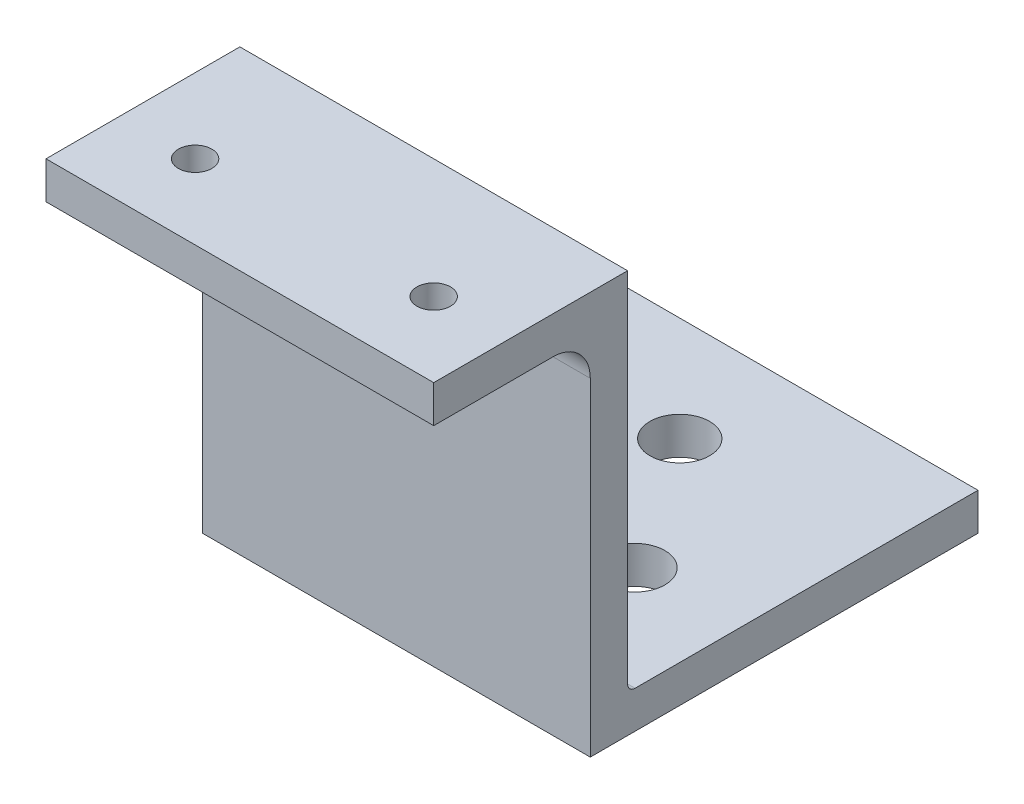
SolidWorks part; units mm, degrees
material "PBT General Purpose"
ref_plane "Front Plane" through (0, 0, 0) normal (0, 0, 1) x (1, 0, 0)
ref_plane "Top Plane" through (0, 0, 0) normal (0, 1, 0) x (1, 0, 0)
ref_plane "Right Plane" through (0, 0, 0) normal (1, 0, 0) x (0, 0, -1)
sketch "Sketch1" plane through (0, 0, 0) normal (0, 1, 0) x (1, 0, 0)
  line L0 (0, 0) -> (40, 0) construction
  line L1 (0, 0) -> (0, 40) construction
  line L2 (40, 0) -> (40, 40) construction
  line L3 (0, 40) -> (40, 40) construction
  line L4 (-1, 41) -> (41, 41)
  line L5 (-1, 41) -> (-1, -1)
  line L6 (41, 41) -> (41, -1)
  line L7 (-1, -1) -> (41, -1)
  line L8 (-6, 46) -> (46, 46)
  line L9 (-6, 46) -> (-6, -6)
  line L10 (46, 46) -> (46, -6)
  line L11 (-6, -6) -> (46, -6)
  dimension "D1" = 40
  dimension "D2" = 40
  dimension "D3" = 1
  dimension "D4" = 1
  dimension "D5" = 1
  dimension "D6" = 1
  dimension "D7" = 5
  dimension "D8" = 5
  dimension "D9" = 5
  dimension "D10" = 5
extrude "Boss-Extrude1" add sketch "Sketch1" along normal blind 5
sketch "Sketch2" plane through (0, 5, 0) normal (0, 1, 0) x (1, 0, 0)
  line L0 (46, -6) -> (46, 46) construction
  line L1 (46, 46) -> (-6, 46) construction
  line L2 (-6, -6) -> (46, -6) construction
  line L3 (-6, 46) -> (-6, -6) construction
  line L4 (46, -6) -> (46, 46)
  line L5 (46, 46) -> (-6, 46)
  line L6 (-6, -6) -> (46, -6)
  line L7 (-6, 46) -> (-6, -6)
extrude "Boss-Extrude2" add sketch "Sketch2" along normal blind 5
sketch "Sketch3" plane through (0, 10, 0) normal (0, 1, 0) x (1, 0, 0)
  line L0 (46, -6) -> (-6, -6)
  line L1 (46, -6) -> (46, -1)
  line L2 (-6, -6) -> (-6, -1)
  line L3 (46, -1) -> (-6, -1)
  dimension "D1" = 5
extrude "Boss-Extrude3" add sketch "Sketch3" along normal blind 44
sketch "Sketch4" plane through (0, 54, 0) normal (0, 1, 0) x (1, 0, 0)
  line L0 (46, -1) -> (-6, -1)
  line L1 (46, -1) -> (46, -27)
  line L2 (-6, -1) -> (-6, -27)
  line L3 (46, -27) -> (-6, -27)
  dimension "D1" = 26
extrude "Boss-Extrude4" add sketch "Sketch4" along normal blind 5
sketch "Sketch5" plane through (0, 59, 0) normal (0, 1, 0) x (1, 0, 0)
  line L0 (46, -17) -> (-6, -17) construction
  line L1 (46, -27) -> (46, -1) construction
  line L2 (-6, -1) -> (-6, -27) construction
  line L3 (-6, -27) -> (46, -27) construction
  circle A0 centre (36, -17) radius 2.25
  circle A1 centre (4, -17) radius 2.25
  dimension "D2" = 10
  dimension "D3" = 4.5
  dimension "D4" = 10
  dimension "D5" = 4.5
  dimension "D1" = 10
extrude "Cut-Extrude1" cut sketch "Sketch5" against normal through all
sketch "Sketch6" plane through (0, 5, 0) normal (0, -1, 0) x (1, 0, 0)
  line L0 (20, -41) -> (20, 1) construction
  line L1 (41, -41) -> (-1, -41) construction
  line L2 (41, -20) -> (-1, -20) construction
  line L3 (41, 1) -> (41, -41) construction
  line L4 (-1, -41) -> (-1, 1) construction
  line L5 (-1, 1) -> (41, 1) construction
ref_plane "Plane1" through (20, 0, 0) normal (1, 0, 0) x (0, 0, 1)
ref_plane "Plane2" through (0, 0, -20) normal (0, 0, 1) x (-1, 0, 0)
fillet "Fillet1" radius 5 1 edges
fillet "Fillet2" radius 1 1 edges
sketch "Sketch7" plane through (0, 5, 0) normal (0, -1, 0) x (1, 0, 0)
  line L0 (20, -41) -> (20, 1) construction
  line L1 (-1, 1) -> (41, 1) construction
  line L2 (41, -41) -> (-1, -41) construction
  line L3 (41, -14) -> (-1, -14) construction
  line L4 (41, 1) -> (41, -41) construction
  line L5 (-1, -41) -> (-1, 1) construction
  circle A0 centre (20, -32) radius 4
  circle A1 centre (32, -14) radius 4
  circle A2 centre (8, -14) radius 4
  dimension "D1" = 8
  dimension "D2" = 9
  dimension "D4" = 8
  dimension "D5" = 8
  dimension "D6" = 9
  dimension "D3" = 15
  dimension "D7" = 9
extrude "Cut-Extrude2" cut sketch "Sketch7" against normal through all
sketch "Sketch8" plane through (0, 0, 0) normal (0, -1, 0) x (1, 0, 0)
  line L0 (-1, 1) -> (41, 1) construction
  line L1 (41, 1) -> (41, -41) construction
  line L2 (41, -41) -> (-1, -41) construction
  line L3 (-1, 1) -> (41, 1)
  line L4 (-6, 6) -> (-6, -46)
  line L5 (-6, -46) -> (46, -46)
  line L6 (46, -46) -> (46, 6)
  line L7 (46, 6) -> (-6, 6)
  line L8 (-6, 6) -> (-6, -46)
  line L9 (-6, -46) -> (46, -46)
  line L10 (46, -46) -> (46, 6)
  line L11 (46, 6) -> (-6, 6)
  line L12 (41, 1) -> (41, -41)
  line L13 (41, -41) -> (-1, -41)
  line L14 (-1, -41) -> (-1, 1) construction
  line L15 (-1, -41) -> (-1, 1)
  dimension "D1" = 0
extrude "Cut-Extrude3" cut sketch "Sketch8" against normal up to surface (5 mm away) up to face at (8, 5, -18)
